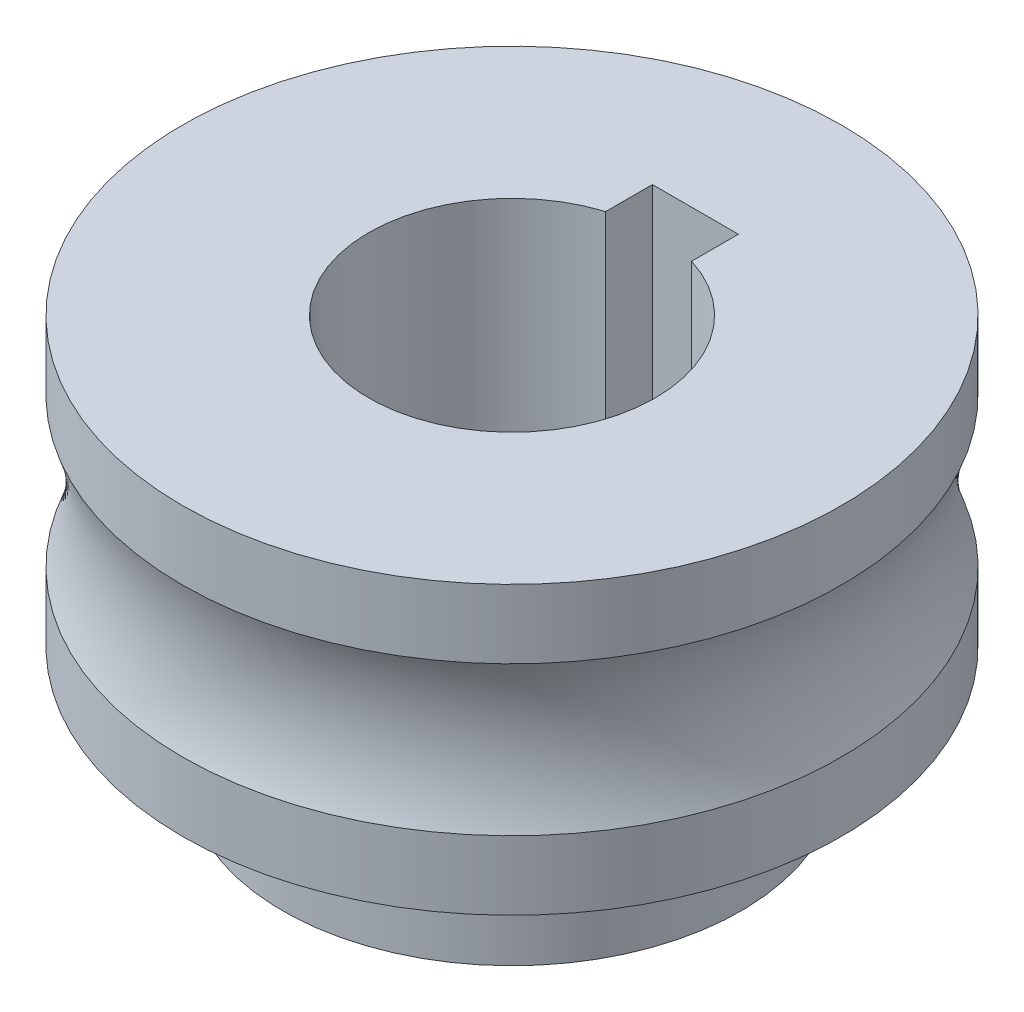
SolidWorks part; units mm, degrees
material "Laiton au plomb 2%, UNS C34200"
ref_plane "Plan de face" through (0, 0, 0) normal (0, 0, 1) x (1, 0, 0)
ref_plane "Plan de dessus" through (0, 0, 0) normal (0, 1, 0) x (1, 0, 0)
ref_plane "Plan de droite" through (0, 0, 0) normal (1, 0, 0) x (0, 0, -1)
sketch "Sketch1" plane through (0, 0, 0) normal (0, 0, 1) x (1, 0, 0)
  line L0 (5, -15) -> (8, -15)
  line L1 (8, -15) -> (8, -5)
  line L2 (8, -5) -> (11.5, -5)
  line L3 (11.5, -5) -> (11.5, -2.5981)
  line L4 (11.5, 5) -> (5, 5)
  line L5 (5, 5) -> (5, -15)
  line L6 (0, -15) -> (0, 19.6952) construction
  line L7 (11.5, 2.5981) -> (11.5, 5)
  line L8 (8, -5) -> (5, -5)
  arc A1 (11.5, 2.5981) -> (11.5, -2.5981) centre (18, 0) ccw
  point P10 (5, 0)
  dimension "D6" = 18
  dimension "D7" = 14
  dimension "D1" = 10
  dimension "D2" = 20
  dimension "D3" = 8
  dimension "D4" = 10
  dimension "D5" = 11.5
  dimension "D8" = 5
revolve "Revolve2" add sketch "Sketch1" angle 360 about L6
ref_plane "Plane1" through (0, 0, 0) normal (0, 1, 0) x (1, 0, 0)
sketch "Esquisse1" plane through (0, 5, 0) normal (0, 1, 0) x (1, 0, 0)
  line L1 (-1.5, 3.6) -> (1.5, 3.6)
  line L2 (-1.5, 3.6) -> (-1.5, 6.4)
  line L3 (-1.5, 6.4) -> (1.5, 6.4)
  line L4 (1.5, 3.6) -> (1.5, 6.4)
  line L5 (-1.5, 3.6) -> (1.5, 6.4) construction
  line L6 (-1.5, 6.4) -> (1.5, 3.6) construction
  circle A0 centre (0, 0) radius 5 construction
  point P0 (0, 5)
  dimension "D1" = 3
  dimension "D2" = 1.4
extrude "Enlèv. mat.-Extru.1" cut sketch "Esquisse1" against normal through all
sketch "Esquisse2" plane through (0, -15, 0) normal (0, -1, 0) x (1, 0, 0)
  circle A0 centre (0, 0) radius 8
  dimension "D1" = 16
extrude "Enlèv. mat.-Extru.2" cut sketch "Esquisse2" against normal offset from surface (6 mm away) 4 up to face at (0, -5, -11.5)
